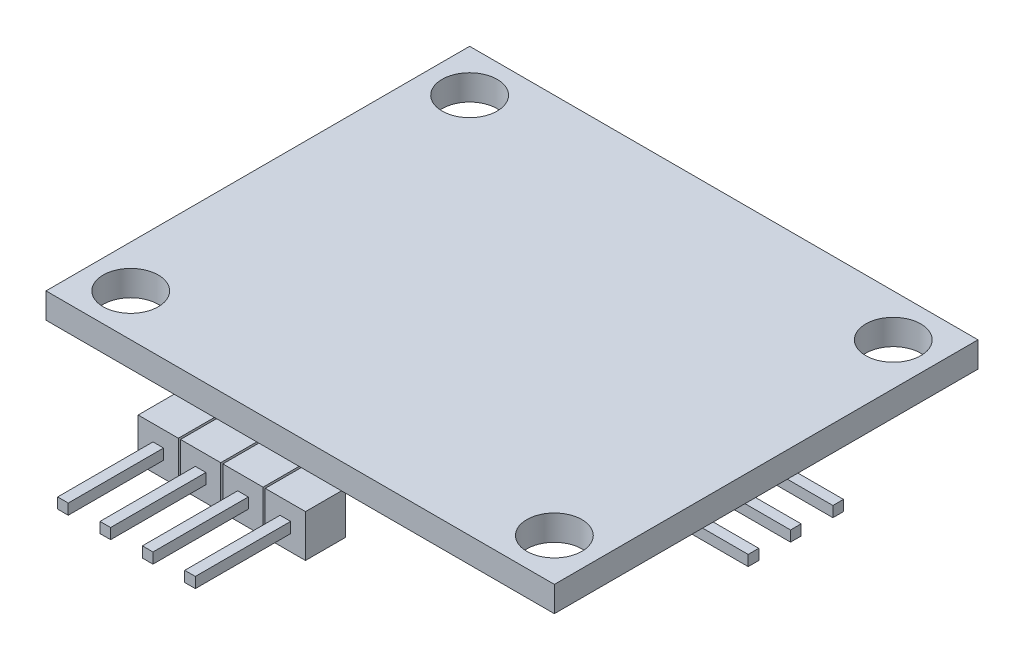
SolidWorks part; units mm, degrees
ref_plane "Front Plane" through (0, 0, 0) normal (0, 0, 1) x (1, 0, 0)
ref_plane "Top Plane" through (0, 0, 0) normal (0, 1, 0) x (1, 0, 0)
ref_plane "Right Plane" through (0, 0, 0) normal (1, 0, 0) x (0, 0, -1)
sketch "Sketch1" plane through (0, 0, 0) normal (0, 1, 0) x (1, 0, 0)
  line L0 (15.24, 25.4) -> (15.24, 0) construction
  line L1 (0, 25.4) -> (30.48, 25.4)
  line L2 (0, 25.4) -> (0, 0)
  line L3 (0, 0) -> (30.48, 0)
  line L4 (30.48, 25.4) -> (30.48, 0)
  line L5 (2.54, 12.7) -> (27.94, 12.7) construction
  line L6 (2.54, 22.86) -> (2.54, 2.54) construction
  line L7 (27.94, 22.86) -> (27.94, 2.54) construction
  circle A0 centre (2.54, 22.86) radius 1.651
  circle A1 centre (27.94, 22.86) radius 1.651
  circle A2 centre (27.94, 2.54) radius 1.651
  circle A3 centre (2.54, 2.54) radius 1.651
  point P13 (15.24, 12.7)
  dimension "D5" = 3.302
  dimension "D1" = 30.48
  dimension "D2" = 25.4
  dimension "D3" = 25.4
  dimension "D4" = 20.32
extrude "Boss-Extrude1" add sketch "Sketch1" along normal blind 1.524
sketch "Sketch2" plane through (0, 1.524, 0) normal (0, 1, 0) x (1, 0, 0)
  line L0 (15.24, 1.524) -> (15.24, 0) construction
  line L1 (8.89, 1.524) -> (11.43, 1.524) construction
  line L2 (11.43, 1.524) -> (13.97, 1.524) construction
  line L3 (13.97, 1.524) -> (16.51, 1.524) construction
  line L4 (16.51, 1.524) -> (19.05, 1.524) construction
  line L5 (19.05, 1.524) -> (21.59, 1.524) construction
  line L6 (0, 0) -> (30.48, 0) construction
  line L7 (21.59, 1.524) -> (24.13, 1.524) construction
  line L8 (22.86, 15.24) -> (22.86, 10.16) construction
  line L9 (22.86, 12.7) -> (30.48, 12.7) construction
  line L10 (30.48, 0) -> (30.48, 25.4) construction
  line L11 (22.86, 10.16) -> (22.86, 1.524) construction
  point P10 (24.13, 12.7)
  dimension "D1" = 2.54
  dimension "D2" = 1.524
  dimension "D3" = 5.08
  dimension "D4" = 1.27
sketch "Sketch3" plane through (0, 0, 0) normal (0, -1, 0) x (-1, 0, 0)
  line L0 (-25.3365, 11.3665) -> (-25.3365, 11.4935) construction
  line L5 (-26.543, 8.9535) -> (-26.543, 11.3665)
  line L6 (-26.543, 8.9535) -> (-24.13, 8.9535)
  line L7 (-24.13, 8.9535) -> (-24.13, 11.3665)
  line L8 (-26.543, 11.3665) -> (-24.13, 11.3665)
  line L9 (-26.543, 11.4935) -> (-26.543, 13.9065)
  line L10 (-26.543, 11.4935) -> (-24.13, 11.4935)
  line L11 (-24.13, 11.4935) -> (-24.13, 13.9065)
  line L12 (-26.543, 13.9065) -> (-24.13, 13.9065)
  line L13 (-26.543, 14.0335) -> (-26.543, 16.4465)
  line L14 (-26.543, 14.0335) -> (-24.13, 14.0335)
  line L15 (-24.13, 14.0335) -> (-24.13, 16.4465)
  line L16 (-26.543, 16.4465) -> (-24.13, 16.4465)
  line L21 (-25.3365, 14.0335) -> (-25.3365, 13.9065) construction
  line L23 (-22.86, 12.7) -> (-30.48, 12.7) construction
  line L24 (-15.3035, -0.9525) -> (-15.1765, -0.9525) construction
  line L25 (-17.7165, 0.254) -> (-15.3035, 0.254)
  line L26 (-17.7165, 0.254) -> (-17.7165, -2.159)
  line L27 (-17.7165, -2.159) -> (-15.3035, -2.159)
  line L28 (-15.3035, 0.254) -> (-15.3035, -2.159)
  line L29 (-15.1765, 0.254) -> (-12.7635, 0.254)
  line L30 (-15.1765, 0.254) -> (-15.1765, -2.159)
  line L31 (-15.1765, -2.159) -> (-12.7635, -2.159)
  line L32 (-12.7635, 0.254) -> (-12.7635, -2.159)
  line L33 (-12.6365, 0.254) -> (-10.2235, 0.254)
  line L34 (-12.6365, 0.254) -> (-12.6365, -2.159)
  line L35 (-12.6365, -2.159) -> (-10.2235, -2.159)
  line L36 (-10.2235, 0.254) -> (-10.2235, -2.159)
  line L37 (-10.0965, 0.254) -> (-7.6835, 0.254)
  line L38 (-10.0965, 0.254) -> (-10.0965, -2.159)
  line L39 (-10.0965, -2.159) -> (-7.6835, -2.159)
  line L40 (-7.6835, 0.254) -> (-7.6835, -2.159)
  line L41 (-12.6365, -0.9525) -> (-12.7635, -0.9525) construction
  line L42 (-10.0965, -0.9525) -> (-10.2235, -0.9525) construction
  line L43 (-15.24, 1.524) -> (-15.24, 0) construction
  line L44 (0, 0) -> (-30.48, 0) construction
  point P27 (-15.24, -0.9525)
  dimension "D1" = 0.127
  dimension "D2" = 0.127
  dimension "D3" = 2.413
  dimension "D4" = 2.413
  dimension "D5" = 0.254
extrude "Boss-Extrude2" add sketch "Sketch3" along normal blind 2.54
sketch "Sketch4" plane through (0, 0, 2.159) normal (0, 0, 1) x (1, 0, 0)
  line L0 (10.0965, -1.27) -> (7.6835, -1.27) construction
  line L1 (7.6835, -2.54) -> (7.6835, 0) construction
  line L2 (10.0965, -2.54) -> (10.0965, 0) construction
  line L5 (8.89, -0.9525) -> (8.89, -1.5875) construction
  line L7 (9.2075, -0.9525) -> (9.2075, -1.5875)
  line L8 (9.2075, -0.9525) -> (8.5725, -0.9525)
  line L9 (8.5725, -0.9525) -> (8.5725, -1.5875)
  line L10 (9.2075, -1.5875) -> (8.5725, -1.5875)
  line L134 (11.7475, -0.9525) -> (11.1125, -0.9525)
  line L135 (11.7475, -0.9525) -> (11.7475, -1.5875)
  line L136 (11.7475, -1.5875) -> (11.1125, -1.5875)
  line L137 (11.1125, -0.9525) -> (11.1125, -1.5875)
  line L138 (14.2875, -0.9525) -> (13.6525, -0.9525)
  line L139 (14.2875, -0.9525) -> (14.2875, -1.5875)
  line L140 (14.2875, -1.5875) -> (13.6525, -1.5875)
  line L141 (13.6525, -0.9525) -> (13.6525, -1.5875)
  line L142 (16.8275, -0.9525) -> (16.1925, -0.9525)
  line L143 (16.8275, -0.9525) -> (16.8275, -1.5875)
  line L144 (16.8275, -1.5875) -> (16.1925, -1.5875)
  line L145 (16.1925, -0.9525) -> (16.1925, -1.5875)
  point P8 (8.89, -1.27)
  dimension "D1" = 0.635
  dimension "D2" = 4
extrude "Boss-Extrude3" add sketch "Sketch4" along normal blind 5.715
sketch "Sketch5" plane through (26.543, 0, 0) normal (1, 0, 0) x (0, 0, -1)
  line L0 (11.3665, -1.27) -> (8.9535, -1.27) construction
  line L3 (8.9535, -2.54) -> (8.9535, 0) construction
  line L4 (11.3665, -2.54) -> (11.3665, 0) construction
  line L5 (10.16, -0.9525) -> (10.16, -1.5875) construction
  line L7 (10.4775, -0.9525) -> (10.4775, -1.5875)
  line L8 (10.4775, -0.9525) -> (9.8425, -0.9525)
  line L9 (9.8425, -0.9525) -> (9.8425, -1.5875)
  line L10 (10.4775, -1.5875) -> (9.8425, -1.5875)
  line L134 (13.0175, -0.9525) -> (12.3825, -0.9525)
  line L135 (13.0175, -0.9525) -> (13.0175, -1.5875)
  line L136 (13.0175, -1.5875) -> (12.3825, -1.5875)
  line L137 (12.3825, -0.9525) -> (12.3825, -1.5875)
  line L138 (15.5575, -0.9525) -> (14.9225, -0.9525)
  line L139 (15.5575, -0.9525) -> (15.5575, -1.5875)
  line L140 (15.5575, -1.5875) -> (14.9225, -1.5875)
  line L141 (14.9225, -0.9525) -> (14.9225, -1.5875)
  line L146 (18.0975, -0.9525) -> (17.4625, -0.9525) [skipped]
  line L147 (18.0975, -0.9525) -> (18.0975, -1.5875) [skipped]
  line L148 (18.0975, -1.5875) -> (17.4625, -1.5875) [skipped]
  line L149 (17.4625, -0.9525) -> (17.4625, -1.5875) [skipped]
  point P8 (10.16, -1.27)
  dimension "D1" = 0.635
  dimension "D2" = 4
extrude "Boss-Extrude4" add sketch "Sketch5" along normal blind 5.715
